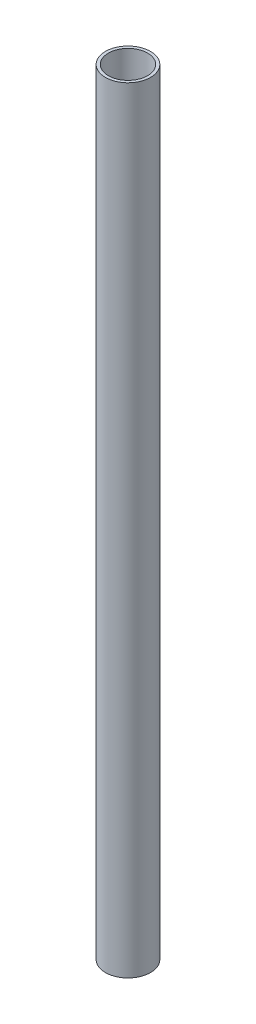
SolidWorks part; units mm, degrees
material "Carbon Fiber"
ref_plane "Front Plane" through (0, 0, 0) normal (0, 0, 1) x (1, 0, 0)
ref_plane "Top Plane" through (0, 0, 0) normal (0, 1, 0) x (1, 0, 0)
ref_plane "Right Plane" through (0, 0, 0) normal (1, 0, 0) x (0, 0, -1)
sketch "Sketch1" plane through (0, 0, 0) normal (0, 1, 0) x (1, 0, 0)
  circle A0 centre (0, 0) radius 5.9055
  circle A1 centre (0, 0) radius 5.1435
  dimension "D1" = 11.811
  dimension "D2" = 0.762
extrude "Boss-Extrude1" add sketch "Sketch1" along normal blind 203.2
